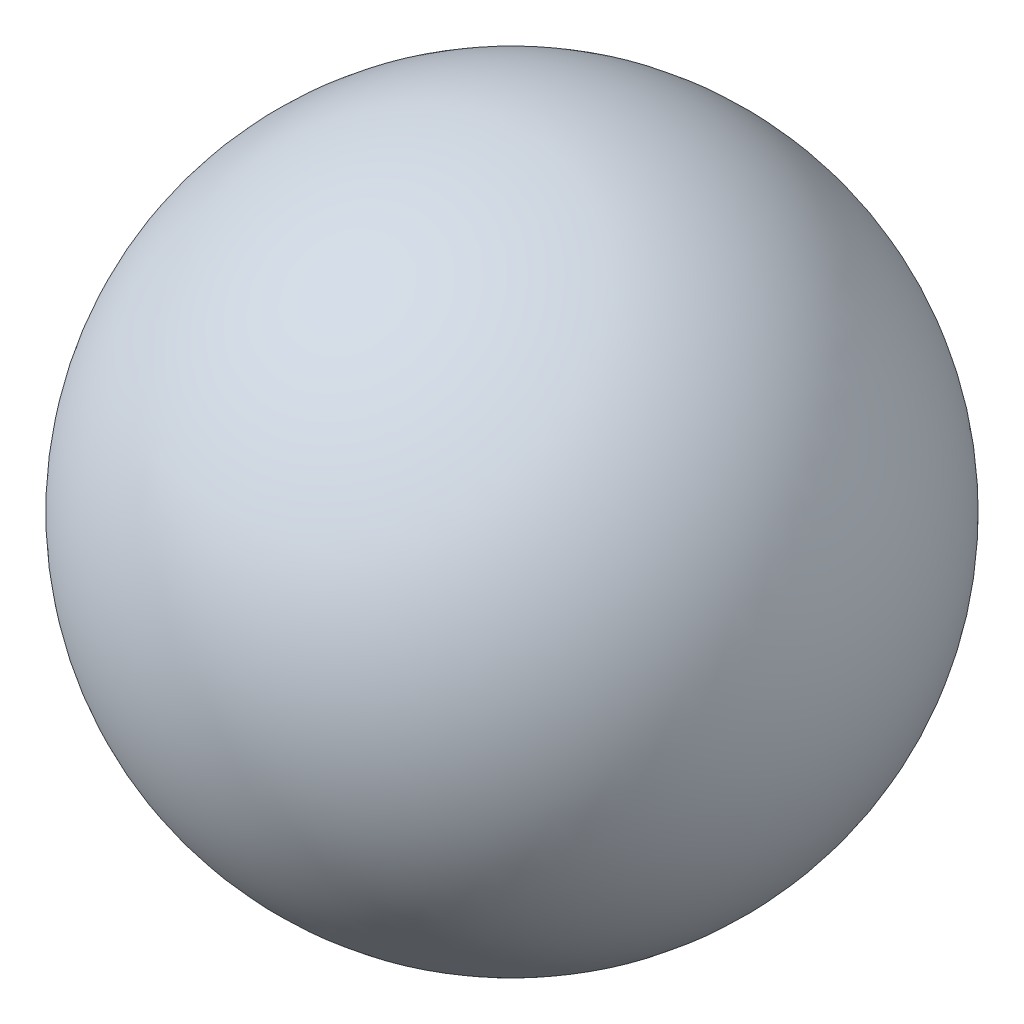
SolidWorks part; units mm, degrees
ref_plane "Front Plane" through (0, 0, 0) normal (0, 0, 1) x (1, 0, 0)
ref_plane "Top Plane" through (0, 0, 0) normal (0, 1, 0) x (1, 0, 0)
ref_plane "Right Plane" through (0, 0, 0) normal (1, 0, 0) x (0, 0, -1)
sketch "Sketch3" plane through (0, 0, 0) normal (0, 0, 1) x (1, 0, 0)
  line L0 (0, 0) -> (0, 15)
  arc A0 (0, 0) -> (0, 15) centre (0, 7.5) ccw
  dimension "D1" = 15
revolve "Revolve1" add sketch "Sketch3" angle 360 about L0
